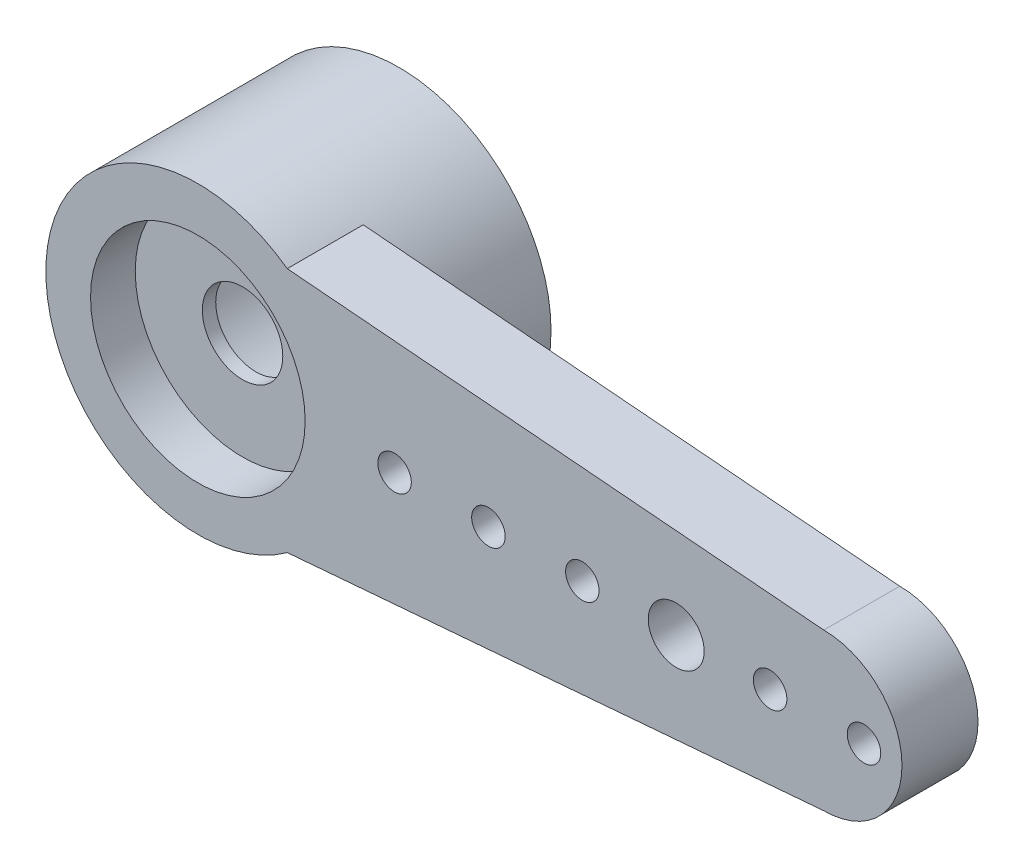
SolidWorks part; units mm, degrees
ref_plane "Přední rovina" through (0, 0, 0) normal (0, 0, 1) x (1, 0, 0)
ref_plane "Horní rovina" through (0, 0, 0) normal (0, 1, 0) x (1, 0, 0)
ref_plane "Pravá rovina" through (0, 0, 0) normal (1, 0, 0) x (0, 0, -1)
sketch "Skica1" plane through (0, 0, 0) normal (0, 0, 1) x (1, 0, 0)
  circle A0 centre (0, 0) radius 3.4
  dimension "D1" = 6.8
extrude "Přidat vysunutím1" add sketch "Skica1" along normal blind 4.5
sketch "Skica2" plane through (0, 0, 0) normal (0, 0, -1) x (-1, 0, 0)
  circle A0 centre (0, 0) radius 2.25
  circle A1 centre (0, 0) radius 3.4 construction
  dimension "D1" = 4.5
extrude "Odebrat vysunutím1" cut sketch "Skica2" against normal blind 3.2
sketch "Skica3" plane through (0, 0, 4.5) normal (0, 0, 1) x (1, 0, 0)
  circle A0 centre (0, 0) radius 2.4
  circle A1 centre (0, 0) radius 3.4 construction
  dimension "D1" = 4.8
extrude "Odebrat vysunutím2" cut sketch "Skica3" against normal blind 1
sketch "Skica4" plane through (0, 0, 3.5) normal (0, 0, 1) x (1, 0, 0)
  circle A0 centre (0, 0) radius 0.9
  dimension "D1" = 1.8
extrude "Odebrat vysunutím3" cut sketch "Skica4" against normal up to surface (0.3 mm away) up to face at (-2.25, 0, 3.2)
sketch "Skica5" plane through (0, 0, 4.5) normal (0, 0, 1) x (1, 0, 0)
  line L0 (14, 1.75) -> (1.9994, 2.75)
  line L1 (14, -1.75) -> (1.9994, -2.75)
  circle A0 centre (14, 0) radius 1.75
  circle A1 centre (0, 0) radius 3.4 construction
  circle A2 centre (0, 0) radius 3.4
  circle M4 centre (0, 0) radius 3.4
  dimension "D2" = 3.5
  dimension "D1" = 14
  dimension "D3" = 5.5
extrude "Přidat vysunutím2" add sketch "Skica5" against normal blind 1.7 contours A0 L0 L1 M4 | A0 A2
sketch "Skica6" plane through (0, 0, 4.5) normal (0, 0, 1) x (1, 0, 0)
  circle A0 centre (4.4, 0) radius 0.375
  dimension "D1" = 0.75
  dimension "D2" = 4.4
extrude "Odebrat vysunutím4" cut sketch "Skica6" against normal up to surface (1.7 mm away) up to face at (8.7873, 0, 2.8)
pattern_linear "LinPole1" count 6 spacing 2.1 along (1, 0, 0) of "Odebrat vysunutím4"
sketch "Skica7" plane through (0, 0, 4.5) normal (0, 0, 1) x (1, 0, 0)
  circle A0 centre (10.7, 0) radius 0.625
  dimension "D1" = 1.25
extrude "Odebrat vysunutím5" cut sketch "Skica7" against normal up to surface (1.7 mm away) up to face at (15.275, 0, 2.8)
